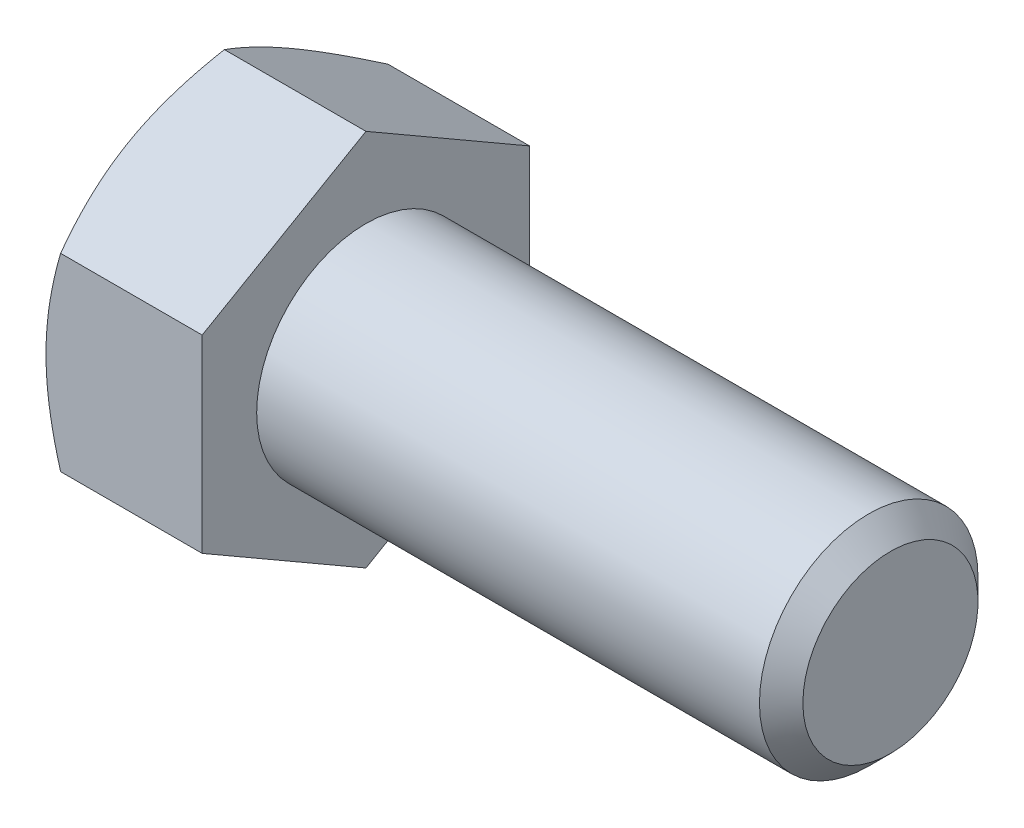
SolidWorks part; units mm, degrees
extrude "BaseHead" add sketch "Sketch1" along normal blind 6.8072
sketch "Sketch1" plane through (0, 0, 0) normal (1, 0, 0) x (0, 0, -1)
  line L0 (7.1374, 4.1208) -> (7.1374, -4.1208)
  line L1 (-7.1374, 4.1208) -> (-7.1374, -4.1208)
  line L2 (7.1374, -4.1208) -> (0, -8.2416)
  line L3 (0, -8.2416) -> (-7.1374, -4.1208)
  line L4 (7.1374, 4.1208) -> (0, 8.2416)
  line L5 (0, 8.2416) -> (-7.1374, 4.1208)
  dimension "Width_flats" = 14.2748
  dimension "D2" = 120
  dimension "D3" = 7.1374
  dimension "D4" = 7.1374
  dimension "D5" = 7.1374
ref_plane "Plane1" through (0, 0, 0) normal (0, 0, 1) x (1, 0, 0)
ref_plane "Plane2" through (0, 0, 0) normal (0, 1, 0) x (1, 0, 0)
ref_plane "Plane3" through (0, 0, 0) normal (1, 0, 0) x (0, 0, -1)
sketch "BodySke" plane through (0, 0, 0) normal (0, 0, 1) x (1, 0, 0)
  line L0 (0, 4.1208) -> (0, -4.1208) construction
  line L1 (0, 0) -> (29.6672, 0)
  line L2 (0, 0) -> (0, 4.7625)
  line L3 (0, 4.7625) -> (28.721, 4.7625)
  line L4 (29.6672, 0) -> (29.6672, 3.8163)
  line L5 (6.8072, 8.2416) -> (6.8072, 4.1208) construction
  line L6 (29.6672, 3.8163) -> (28.721, 4.7625)
  line L7 (0, 0) -> (96.52, 0) construction
  line L8 (29.6672, -3.8163) -> (28.721, -4.7625) construction
  line L9 (0, -4.7625) -> (28.721, -4.7625) construction
  line L10 (8.3947, 15.24) -> (8.3947, -2.54) construction
  line L11 (4.2672, 15.24) -> (4.2672, -2.54) construction
  line L12 (6.8072, 4.1208) -> (6.8072, -4.1208) construction
  dimension "Diameter" = 9.525
revolve "BaseBody" add sketch "BodySke" angle 360 about L7
cosmetic thread "ThreadCosmetic" [suppressed] parameters "Thread_length"=21.2725, "Thread_minor"=7.6327
sketch "Sketch3" plane through (0, 0, 0) normal (0, 0, 1) x (1, 0, 0)
  line L0 (0, 7.1374) -> (4.3037, 14.5916)
  line L1 (0, 8.2416) -> (0, 4.1208) construction
  line L2 (4.3037, 14.5916) -> (4.3037, 20.9416)
  line L3 (4.3037, 20.9416) -> (-12.7, 20.9416)
  line L4 (-12.7, 20.9416) -> (-12.7, 7.1374)
  line L5 (-12.7, 7.1374) -> (0, 7.1374)
  line L6 (0, 0) -> (99.06, 0) construction
  line L7 (6.8072, 8.2416) -> (0, 8.2416) construction
  dimension "D1" = 7.1374
  dimension "D2" = 6.35
  dimension "D3" = 12.7
  dimension "D4" = 6.35
  dimension "Head_ch_ang" = 30
revolve "HeadChamfer" cut sketch "Sketch3" angle 360 about L6
fillet "HeadFillet" [suppressed] radius 0.762
sketch "ThdSchSke" plane through (0, 0, 0) normal (0, 0, 1) x (1, 0, 0)
  line L0 (8.3947, -3.8163) -> (7.7322, -4.7625)
  line L1 (8.3947, -3.8163) -> (9.0572, -4.7625)
  line L2 (9.0572, -4.7625) -> (9.0572, -5.9531)
  line L3 (-3.175, 0) -> (5.1513, 0) construction
  line L5 (9.0572, -5.9531) -> (7.7322, -5.9531)
  line L6 (7.7322, -5.9531) -> (7.7322, -4.7625)
  dimension "Thread_minor" = 7.6327
  dimension "Diameter" = 9.525
  dimension "Start" = 8.3947
revolve "ThreadSchematic" [suppressed] cut sketch "ThdSchSke" angle 360 about L3
pattern_linear "ThdSchPat" [suppressed]
equation "\"D3@Sketch1\" = \"Width_flats@Sketch1\" / 2"
equation "\"D4@Sketch1\" = \"D3@Sketch1\""
equation "\"D5@Sketch1\" = \"D4@Sketch1\""
equation "\"Thread_minor@ThreadCosmetic\" = \"Minor_dia@BodySke\""
equation "\"D1@Sketch3\" = \"Width_flats@Sketch1\" / 2"
equation "\"Thread_length@ThreadCosmetic\" = ((sgn( (\"Length@BodySke\" - \"Advance@BodySke\" ) - \"Thread_nom@BodySke\" )-1)*( (\"Length@BodySke\" - \"Advance@BodySke\" ) - \"Thread_nom@BodySke\" ))/-2+ \"Thread_nom@BodySke\""
equation "\"Thread_minor@ThdSchSke\" = \"Minor_dia@BodySke\""
equation "\"Diameter@ThdSchSke\" = \"Diameter@BodySke\""
equation "\"Overcut@ThdSchSke\" = \"Diameter@BodySke\" * 1.25"
equation "\"Start@ThdSchSke\" = \"Head_ht@BaseHead\" + \"Length@BodySke\" - \"Thread_length@ThreadCosmetic\"  '---Non-countersunk---"
equation "\"Num_threads@ThdSchPat\" = int( \"Thread_length@ThreadCosmetic\" / \"Advance@BodySke\" + 0.999 )  + 1"
equation "\"Advance@ThdSchPat\" = \"Thread_length@ThreadCosmetic\" /  (\"Num_threads@ThdSchPat\" - 1) 'relax it"
equation "\"Num_threads@ThdSchPat\" = \"Num_threads@ThdSchPat\" - sgn( \"Num_threads@ThdSchPat\" - 1) '---chamfered tips only---"
